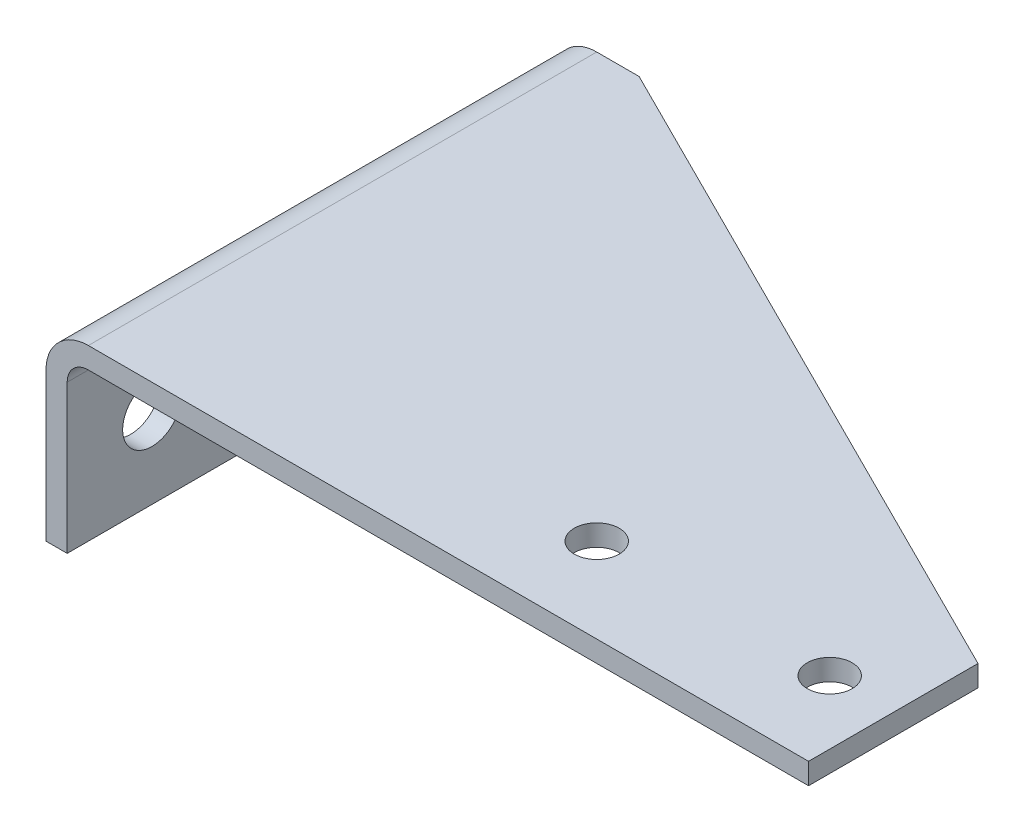
SolidWorks part; units mm, degrees
material "ASTM A36"
ref_plane "Front" through (0, 0, 0) normal (0, 0, 1) x (1, 0, 0)
ref_plane "Top" through (0, 0, 0) normal (0, 1, 0) x (1, 0, 0)
ref_plane "Side" through (0, 0, 0) normal (1, 0, 0) x (0, 0, -1)
sketch "Sketch1" plane through (0, 0, 0) normal (0, 0, 1) x (1, 0, 0)
  line L0 (228.6, 0) -> (12.7, 0)
  line L1 (0, -12.7) -> (0, -57.15)
  line L2 (0, -57.15) -> (6.35, -57.15)
  line L3 (6.35, -57.15) -> (6.35, -12.7)
  line L4 (12.7, -6.35) -> (228.6, -6.35)
  line L5 (228.6, -6.35) -> (228.6, 0)
  line L6 (50, 0) -> (-50, 0) construction
  arc A0 (12.7, 0) -> (0, -12.7) centre (12.7, -12.7) ccw
  arc A1 (6.35, -12.7) -> (12.7, -6.35) centre (12.7, -12.7) cw
  dimension "D3" = 6.35
  dimension "D1" = 228.6
  dimension "D2" = 57.15
  dimension "D4" = 6.35
extrude "Extrude1" add sketch "Sketch1" against normal mid plane 254
sketch "Sketch2" plane through (0, 0, 0) normal (0, 1, 0) x (1, 0, 0)
  line L0 (25.4, 127) -> (228.6, 25.4)
  line L1 (228.6, 127) -> (12.7, 127) construction
  line L2 (228.6, 127) -> (228.6, -127) construction
  line L3 (0, -50) -> (0, 50) construction
  line L4 (-50, 0) -> (50, 0) construction
  line L5 (0, 0) -> (258.8616, 0) construction
  line L6 (228.6, 25.4) -> (228.6, 127)
  line L7 (228.6, 127) -> (25.4, 127)
  line L8 (25.4, -127) -> (228.6, -25.4)
  line L9 (228.6, -127) -> (25.4, -127)
  line L10 (228.6, -25.4) -> (228.6, -127)
  line L11 (0, 0) -> (139.7, 0) construction
  line L12 (139.7, 0) -> (209.55, 0) construction
  circle A2 centre (209.55, 0) radius 6.731
  circle A3 centre (139.7, 0) radius 6.731
  dimension "D5" = 69.85
  dimension "D6" = 13.462
  dimension "D1" = 25.4
  dimension "D2" = 25.4
  dimension "D3" = 25.4
  dimension "D4" = 139.7
extrude "Cut-Chamfer" cut sketch "Sketch2" along normal blind 508 and the other way through all
sketch "Sketch3" plane through (0, 0, 0) normal (1, 0, 0) x (0, 0, -1)
  line L0 (101.6, -33.3375) -> (0, -33.3375) construction
  line L2 (50, 0) -> (-50, 0) construction
  line L3 (-14.7043, -93.6625) -> (186.8542, -93.6625) construction
  line L4 (0, 50) -> (0, -50) construction
  line L5 (0, -33.3375) -> (-101.6, -33.3375) construction
  line L6 (-101.6, -33.3375) -> (-101.6, -153.9875) construction
  line L7 (-101.6, -153.9875) -> (0, -153.9875) construction
  circle A0 centre (0, -33.3375) radius 8.763
  circle A1 centre (101.6, -33.3375) radius 8.763
  circle A2 centre (0, -153.9875) radius 8.763
  circle A3 centre (101.6, -153.9875) radius 8.763
  circle A4 centre (-101.6, -33.3375) radius 8.763
  circle A5 centre (-101.6, -153.9875) radius 8.763
  dimension "D2" = 101.6
  dimension "D3" = 17.526
  dimension "D1" = 101.6
  dimension "D4" = 33.3375
  dimension "D5" = 93.6625
extrude "Cut-Holes" cut sketch "Sketch3" along normal through all
sketch "Sketch4" plane through (0, 0, 0) normal (0, 1, 0) x (1, 0, 0)
  line L0 (228.6, 25.4) -> (0, 25.4)
  line L1 (0, 127) -> (0, -127) construction
sketch "Sketch5" plane through (0, 0, 0) normal (0, 1, 0) x (1, 0, 0)
  line L0 (228.6, -25.4) -> (0, -25.4)
  point P3 (0, 0)
  dimension "D1" = 228.6
extrude "Cut-LH" cut sketch "Sketch5" against normal through all and the other way through all
extrude "Cut-RH" [suppressed] cut sketch "Sketch4" against normal through all and the other way through all flip side to cut
